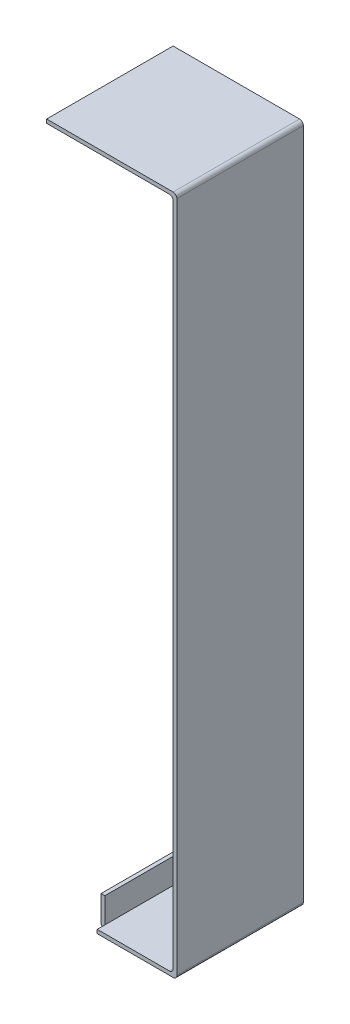
SolidWorks part; units mm, degrees
ref_plane "前视基准面" through (0, 0, 0) normal (0, 0, 1) x (1, 0, 0)
ref_plane "上视基准面" through (0, 0, 0) normal (0, 1, 0) x (1, 0, 0)
ref_plane "右视基准面" through (0, 0, 0) normal (1, 0, 0) x (0, 0, -1)
sketch "草图1" plane through (0, 0, 0) normal (0, 0, 1) x (1, 0, 0)
  line L0 (44.3546, 43.9726) -> (15.8546, 43.9726)
  line L1 (15.8546, 43.9726) -> (-4.1454, 43.9726)
  line L2 (45.8546, 42.4726) -> (45.8546, -36.0274)
  line L3 (45.8546, -36.0274) -> (45.8546, -212.0274)
  line L4 (45.8546, -212.0274) -> (45.8546, -220.5274)
  line L16 (45.8546, 45.4726) -> (-4.1454, 45.4726)
  line L17 (-4.1454, 45.4726) -> (-4.1454, 43.9726)
  line L18 (14.3546, -223.5274) -> (45.8546, -223.5274)
  line L19 (47.3546, -222.0274) -> (47.3546, 43.9726)
  line L20 (44.3546, -222.0274) -> (15.8546, -222.0274)
  line L21 (15.8546, -222.0274) -> (15.8546, -212.0274)
  line L22 (15.8546, -212.0274) -> (14.3546, -212.0274)
  line L23 (14.3546, -212.0274) -> (14.3546, -223.5274)
  arc A0 (45.8546, 45.4726) -> (47.3546, 43.9726) centre (45.8546, 43.9726) cw
  arc A1 (45.8546, 42.4726) -> (44.3546, 43.9726) centre (44.3546, 42.4726) ccw
  arc A2 (45.8546, -223.5274) -> (47.3546, -222.0274) centre (45.8546, -222.0274) ccw
  arc A3 (44.3546, -222.0274) -> (45.8546, -220.5274) centre (44.3546, -220.5274) ccw
  dimension "D1" = 1.5
  dimension "D2" = 1.5
  dimension "D3" = 1.5
extrude "凸台-拉伸2" add sketch "草图1" along normal blind 50
sketch "草图2" plane through (14.3546, 0, 0) normal (-1, 0, 0) x (0, 0, 1)
  line L0 (50, -223.5274) -> (47, -223.5274)
  line L1 (50, -223.5274) -> (0, -223.5274) construction
  line L2 (47, -223.5274) -> (47, -212.0274)
  line L3 (50, -212.0274) -> (0, -212.0274) construction
  line L4 (47, -212.0274) -> (50, -212.0274)
  line L5 (50, 42.4726) -> (50, -220.5274) construction
  line L6 (50, -212.0274) -> (50, -223.5274)
  line L7 (25, -223.5274) -> (25, -153.8118) construction
  line L8 (0, -212.0274) -> (0, -223.5274)
  line L9 (3, -212.0274) -> (0, -212.0274)
  line L10 (3, -223.5274) -> (3, -212.0274)
  line L11 (0, -223.5274) -> (3, -223.5274)
extrude "切除-拉伸1" cut sketch "草图2" against normal blind 1.5
fillet "圆角1" radius 1.5 3 edges at (14.3546, -223.5274, 25) (15.1046, -223.5274, 47) (15.1046, -223.5274, 3)
